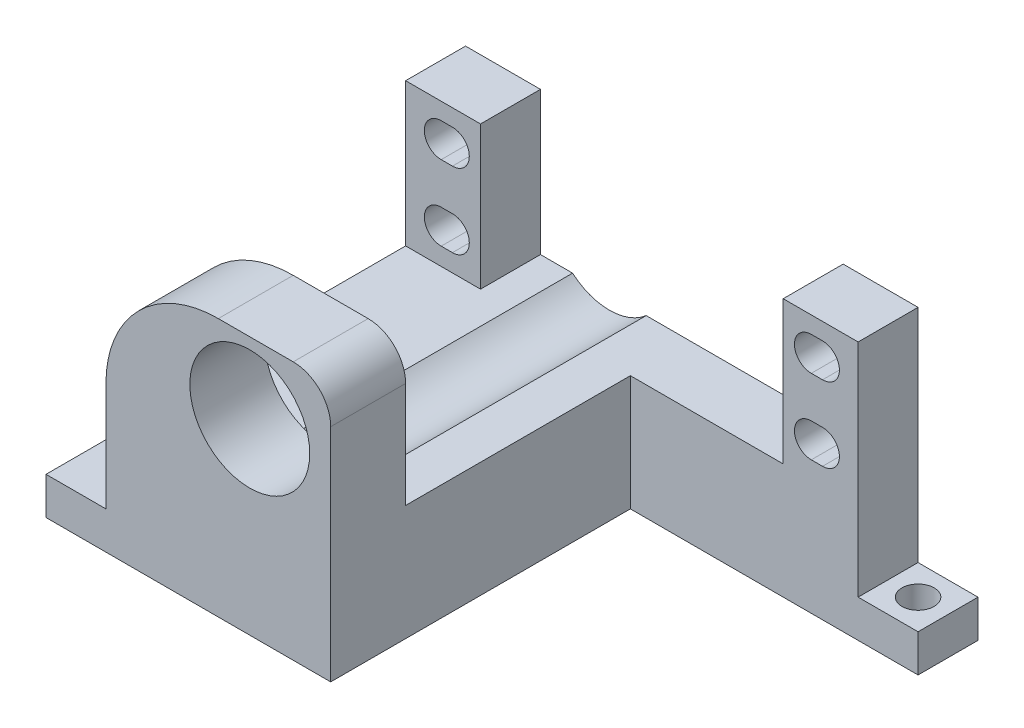
SolidWorks part; units mm, degrees
ref_plane "Front Plane" through (0, 0, 0) normal (0, 0, 1) x (1, 0, 0)
ref_plane "Top Plane" through (0, 0, 0) normal (0, 1, 0) x (1, 0, 0)
ref_plane "Right Plane" through (0, 0, 0) normal (1, 0, 0) x (0, 0, -1)
sketch "Sketch6" plane through (0, 0, 0) normal (0, 0, 1) x (1, 0, 0)
  line L0 (-16.084, 11.3857) -> (-16.084, -7.7143)
  line L1 (-16.084, -7.7143) -> (24.316, -7.7143)
  line L2 (24.316, -7.7143) -> (24.316, 11.3857)
  line L3 (24.316, 11.3857) -> (34.316, 11.3857)
  line L4 (34.316, 11.3857) -> (34.316, -23.1143)
  line L5 (34.316, -23.1143) -> (-26.084, -23.1143)
  line L6 (-26.084, -23.1143) -> (-26.084, 11.3857)
  line L7 (-26.084, 11.3857) -> (-16.084, 11.3857)
  line L8 (-20.584, 11.3857) -> (-20.584, -23.1143) construction
  line L9 (-19.834, 6.8857) -> (-21.334, 6.8857) construction
  line L10 (-19.834, 4.6357) -> (-21.334, 4.6357)
  line L11 (-19.834, 9.1357) -> (-21.334, 9.1357)
  line L12 (-19.834, -3.1143) -> (-21.334, -3.1143) construction
  line L13 (-19.834, -5.3643) -> (-21.334, -5.3643)
  line L14 (-19.834, -0.8643) -> (-21.334, -0.8643)
  line L15 (4.116, -7.7143) -> (4.116, 11.6799) construction
  line L16 (28.066, -3.1143) -> (29.566, -3.1143) construction
  line L17 (28.066, -5.3643) -> (29.566, -5.3643)
  line L18 (28.066, -0.8643) -> (29.566, -0.8643)
  line L19 (28.066, 6.8857) -> (29.566, 6.8857) construction
  line L20 (28.066, 4.6357) -> (29.566, 4.6357)
  line L21 (28.066, 9.1357) -> (29.566, 9.1357)
  arc A0 (-19.834, 4.6357) -> (-19.834, 9.1357) centre (-19.834, 6.8857) ccw
  arc A1 (-21.334, 9.1357) -> (-21.334, 4.6357) centre (-21.334, 6.8857) ccw
  arc A2 (-19.834, -5.3643) -> (-19.834, -0.8643) centre (-19.834, -3.1143) ccw
  arc A3 (-21.334, -0.8643) -> (-21.334, -5.3643) centre (-21.334, -3.1143) ccw
  arc A4 (28.066, -5.3643) -> (28.066, -0.8643) centre (28.066, -3.1143) cw
  arc A5 (29.566, -0.8643) -> (29.566, -5.3643) centre (29.566, -3.1143) cw
  arc A6 (28.066, 4.6357) -> (28.066, 9.1357) centre (28.066, 6.8857) cw
  arc A7 (29.566, 9.1357) -> (29.566, 4.6357) centre (29.566, 6.8857) cw
  point P12 (-20.584, 6.8857)
  point P18 (-20.584, -3.1143)
  point P28 (28.816, -3.1143)
  point P35 (28.816, 6.8857)
  point P40 (-16.084, 12.2857)
  dimension "D11" = 1.5
  dimension "D12" = 1.5
  dimension "D1" = 10
  dimension "D2" = 10
  dimension "D3" = 40.4
  dimension "D4" = 19.1
  dimension "D5" = 19.1
  dimension "D6" = 15.4
  dimension "D7" = 4.5
  dimension "D8" = 10
  dimension "D9" = 4.5
  dimension "D10" = 4.5
  dimension "D13" = 4.6
extrude "Boss-Extrude1" add sketch "Sketch6" along normal blind 8
sketch "Sketch7" plane through (0, 0, 8) normal (0, 0, 1) x (1, 0, 0)
  line L0 (-26.084, -23.1143) -> (34.316, -23.1143) construction
  line L1 (-26.084, -7.7143) -> (3.916, -7.7143)
  line L2 (-26.084, -7.7143) -> (-26.084, -23.1143)
  line L3 (-26.084, -23.1143) -> (3.916, -23.1143)
  line L4 (3.916, -7.7143) -> (3.916, -23.1143)
  line L5 (-26.084, 11.3857) -> (-26.084, -23.1143) construction
  line L6 (24.316, -7.7143) -> (-16.084, -7.7143) construction
  point P7 (0, 0)
  point P8 (-25.4023, -8.9464)
  point P11 (14.7803, -8.9551)
  dimension "D1" = 30
extrude "Boss-Extrude2" add sketch "Sketch7" along normal blind 40
sketch "Sketch8" plane through (0, -7.7143, 0) normal (0, 1, 0) x (1, 0, 0)
  line L0 (3.916, -48) -> (3.916, -8) construction
  line L1 (-26.084, -48) -> (3.916, -48)
  line L2 (-26.084, -48) -> (-26.084, -38)
  line L3 (-26.084, -38) -> (3.916, -38)
  line L4 (3.916, -48) -> (3.916, -38)
  dimension "D1" = 10
extrude "Boss-Extrude3" add sketch "Sketch8" along normal up to surface (19.1 mm away) up to face at (-21.084, 11.3857, 4)
sketch "Sketch9" plane through (0, 0, 48) normal (0, 0, 1) x (1, 0, 0)
  line L0 (3.916, 11.3857) -> (-26.084, 11.3857) construction
  line L1 (-26.084, 11.3857) -> (-26.084, -23.1143) construction
  circle A0 centre (-6.884, 1.8857) radius 8
  dimension "D1" = 9.5
  dimension "D2" = 19.2
  dimension "D3" = 16
extrude "Cut-Extrude1" cut sketch "Sketch9" against normal up to surface (10 mm away) up to face at (-11.084, 1.8357, 38)
fillet "Fillet2" radius 15 1 edges at (-26.084, 11.3857, 43)
fillet "Fillet3" radius 5 1 edges at (3.916, 11.3857, 43)
sketch "Sketch11" plane through (0, 0, 0) normal (0, 0, -1) x (-1, 0, 0)
  line L0 (6.884, 1.8857) -> (6.884, -25.4823) construction
  circle A1 centre (6.884, -2.0448) radius 7.5
  dimension "D1" = 15
extrude "Cut-Extrude2" cut sketch "Sketch11" against normal up to surface (38 mm away) up to face at (1.116, 1.8857, 38)
sketch "Sketch14" plane through (34.316, 0, 0) normal (1, 0, 0) x (0, 0, -1)
  line L0 (0, -23.1143) -> (0, 11.3857) construction
  line L1 (-8, -23.1143) -> (0, -23.1143)
  line L2 (-8, -23.1143) -> (-8, -18.1143)
  line L3 (-8, -18.1143) -> (0, -18.1143)
  line L4 (0, -23.1143) -> (0, -18.1143)
  dimension "D1" = 5
extrude "Boss-Extrude5" add sketch "Sketch14" along normal blind 8
sketch "Sketch15" plane through (-26.084, 0, 0) normal (-1, 0, 0) x (0, 0, 1)
  line L0 (48, -3.6143) -> (48, -23.1143) construction
  line L1 (0, -23.1143) -> (48, -23.1143)
  line L2 (0, -23.1143) -> (0, -18.1143)
  line L3 (0, -18.1143) -> (48, -18.1143)
  line L4 (48, -23.1143) -> (48, -18.1143)
  dimension "D1" = 5
extrude "Boss-Extrude6" add sketch "Sketch15" along normal blind 8
sketch "Sketch16" plane through (0, -18.1143, 0) normal (0, 1, 0) x (1, 0, 0)
  line L0 (-30.084, 0) -> (-30.084, -48) construction
  line L1 (-34.084, 0) -> (-26.084, 0) construction
  line L2 (-34.084, -48) -> (-26.084, -48) construction
  line L3 (34.316, 0) -> (42.316, -8) construction
  line L4 (34.316, -8) -> (42.316, 0) construction
  line L5 (42.316, 0) -> (34.316, 0) construction
  circle A0 centre (-30.084, -11) radius 2.15
  circle A1 centre (-30.084, -36) radius 2.15
  circle A2 centre (38.316, -4) radius 2.15
  dimension "D1" = 4.3
  dimension "D2" = 4.3
  dimension "D3" = 25
  dimension "D4" = 12
  dimension "D5" = 4.3
extrude "Cut-Extrude4" cut sketch "Sketch16" against normal up to surface (5 mm away) up to face at (4.0493, -23.1143, 18.6667)
